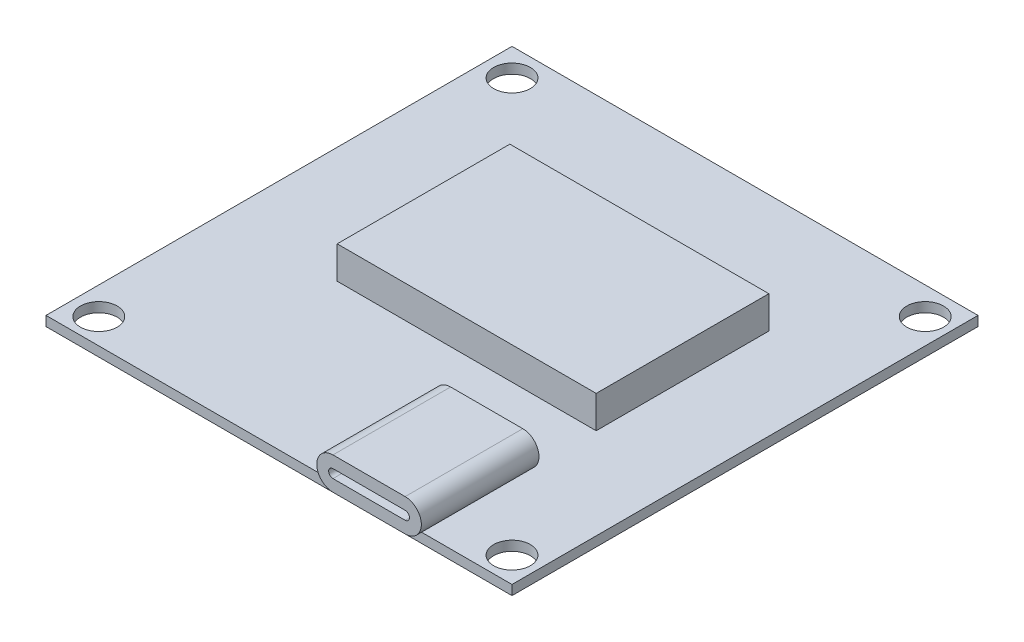
SolidWorks part; units mm, degrees
ref_plane "Front Plane" through (0, 0, 0) normal (0, 0, 1) x (1, 0, 0)
ref_plane "Top Plane" through (0, 0, 0) normal (0, 1, 0) x (1, 0, 0)
ref_plane "Right Plane" through (0, 0, 0) normal (1, 0, 0) x (0, 0, -1)
sketch "Sketch1" plane through (0, 0, 0) normal (0, 1, 0) x (1, 0, 0)
  line L1 (0, 0) -> (43.18, 0)
  line L2 (0, 0) -> (0, 43.18)
  line L3 (0, 43.18) -> (43.18, 43.18)
  line L4 (43.18, 0) -> (43.18, 43.18)
  dimension "D1" = 43.18
  dimension "D2" = 43.18
extrude "Boss-Extrude1" add sketch "Sketch1" along normal blind 0.9
sketch "Sketch2" plane through (0, 0.9, 0) normal (0, 1, 0) x (1, 0, 0)
  line L0 (43.18, 0) -> (43.18, 43.18) construction
  line L1 (43.18, 43.18) -> (0, 43.18) construction
  line L2 (0, 43.18) -> (0, 0) construction
  circle A0 centre (2.54, 40.64) radius 1.7
  point P2 (21.59, 21.59)
  point P5 (43.18, 21.59)
  point P8 (21.59, 43.18)
  dimension "D2" = 3.4
  dimension "D1" = 2.54
  dimension "D3" = 2.54
extrude "Cut-Extrude1" cut sketch "Sketch2" against normal up to next (0.9 mm away)
pattern_circular "CirPattern1" count 4 every 90 about axis through (21.6832, 0, -21.4968) along (0, 1, 0) of "Cut-Extrude1"
sketch "Sketch4" plane through (0, 0, 0) normal (0, 0, 1) x (1, 0, 0)
  line L0 (27.49, 2.4) -> (34.18, 2.4) construction
  line L1 (27.49, 3.9) -> (34.18, 3.9)
  line L2 (27.49, 0.9) -> (34.18, 0.9)
  line L3 (0, 0.9) -> (43.18, 0.9) construction
  line L4 (27.49, 2.4) -> (34.18, 2.4) construction
  line L5 (27.49, 2.8) -> (34.18, 2.8)
  line L6 (27.49, 2) -> (34.18, 2)
  arc A0 (27.49, 3.9) -> (27.49, 0.9) centre (27.49, 2.4) ccw
  arc A1 (34.18, 0.9) -> (34.18, 3.9) centre (34.18, 2.4) ccw
  arc A2 (27.49, 2.8) -> (27.49, 2) centre (27.49, 2.4) ccw
  arc A3 (34.18, 2) -> (34.18, 2.8) centre (34.18, 2.4) ccw
  point P2 (30.835, 2.4)
  point P12 (30.835, 2.4)
  dimension "D1" = 9
  dimension "D2" = 6.69
  dimension "D3" = 3
  dimension "D4" = 0.8
extrude "Boss-Extrude2" add sketch "Sketch4" along normal blind 0.9 and the other way blind 10
sketch "Sketch5" plane through (0, 0.9, 0) normal (0, 1, 0) x (1, 0, 0)
  line L1 (34.7477, 32.2326) -> (10.7477, 32.2326)
  line L2 (34.7477, 32.2326) -> (34.7477, 16.2326)
  line L3 (34.7477, 16.2326) -> (10.7477, 16.2326)
  line L4 (10.7477, 32.2326) -> (10.7477, 16.2326)
  point P4 (37.8158, 32.9996)
  point P5 (34.7477, 32.2326)
  dimension "D1" = 24
  dimension "D2" = 16
extrude "Boss-Extrude3" add sketch "Sketch5" along normal blind 3
